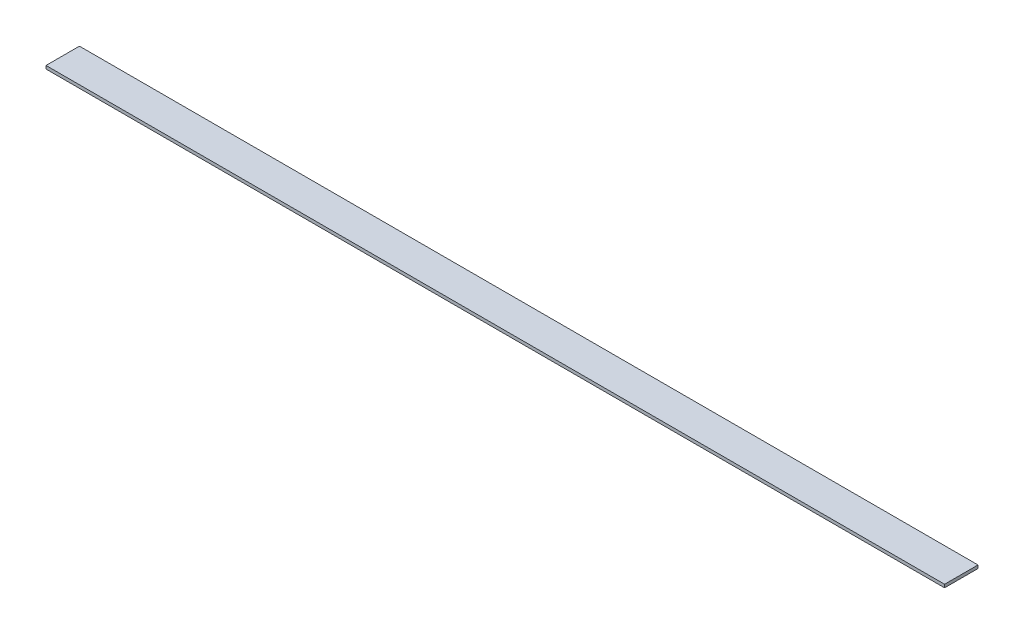
SolidWorks part; units mm, degrees
ref_plane "Front Plane" through (0, 0, 0) normal (0, 0, 1) x (1, 0, 0)
ref_plane "Top Plane" through (0, 0, 0) normal (0, 1, 0) x (1, 0, 0)
ref_plane "Right Plane" through (0, 0, 0) normal (1, 0, 0) x (0, 0, -1)
sketch "Sketch1" plane through (0, 0, 0) normal (0, 1, 0) x (1, 0, 0)
  line L1 (-215, 8) -> (215, 8)
  line L2 (-215, 8) -> (-215, -8)
  line L3 (-215, -8) -> (215, -8)
  line L4 (215, 8) -> (215, -8)
  line L5 (-215, 8) -> (215, -8) construction
  line L6 (-215, -8) -> (215, 8) construction
  point P0 (0, 0)
  dimension "D1" = 16
  dimension "D2" = 430
extrude "Boss-Extrude1" add sketch "Sketch1" along normal blind 1.5
